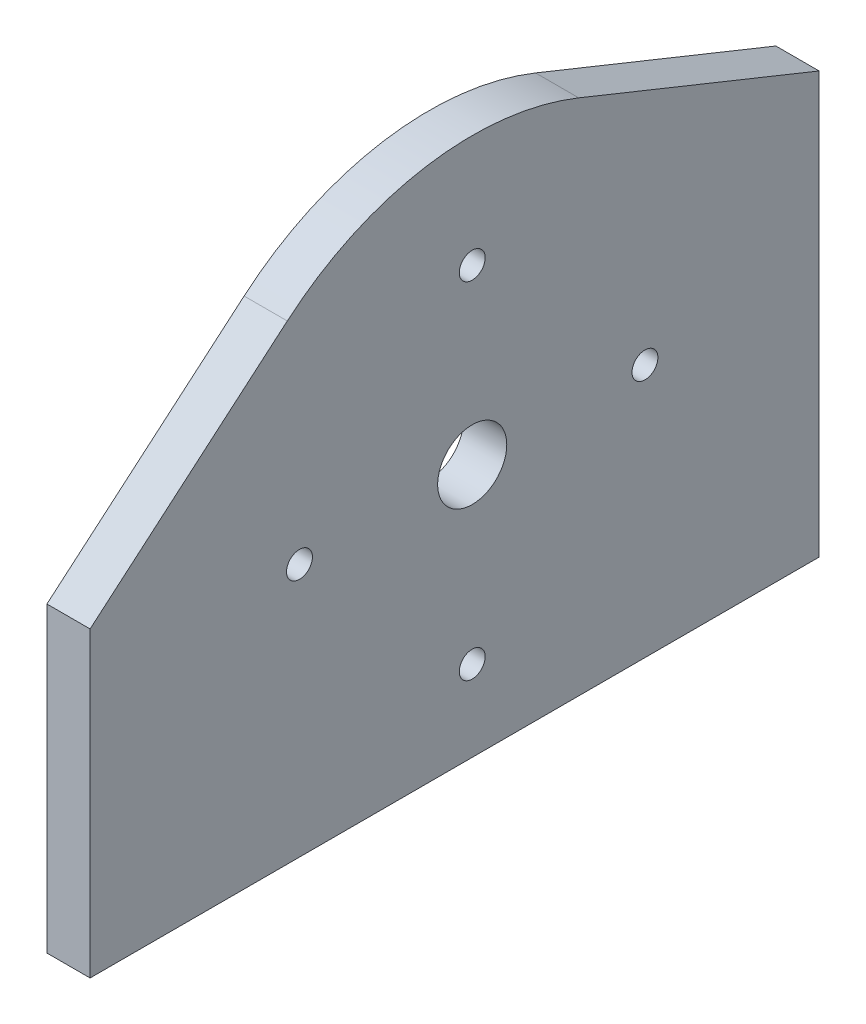
SolidWorks part; units mm, degrees
material "PMMA"
ref_plane "Piano frontale" through (0, 0, 0) normal (0, 0, 1) x (1, 0, 0)
ref_plane "Piano superiore" through (0, 0, 0) normal (0, 1, 0) x (1, 0, 0)
ref_plane "Piano destro" through (0, 0, 0) normal (1, 0, 0) x (0, 0, -1)
sketch "Model" plane through (0, 0, 0) normal (1, 0, 0) x (0, 0, -1)
  line L0 (67.9402, 99.4804) -> (217.5257, 99.4804)
  line L1 (217.5257, 99.4804) -> (217.5258, 94.516)
  line L2 (217.5258, 94.516) -> (67.9406, 94.5157)
  line L3 (67.9406, 94.5157) -> (67.9402, 99.4804)
  line L4 (75.701, 145.6492) -> (169.4508, 145.6492)
  line L5 (169.4508, 145.6492) -> (169.4508, 140.6845)
  line L6 (169.4508, 140.6845) -> (75.7013, 140.6845)
  line L7 (75.7013, 140.6845) -> (75.701, 145.6492)
  line L8 (277.8427, 54.3742) -> (278.3063, 54.3694)
  line L9 (278.3063, 54.3694) -> (7.5827, 54.3742)
  line L10 (-9.9912, 108.2246) -> (89.8382, 182.1486)
  line L11 (107.8333, 184.8972) -> (289.0756, 111.8678)
  line L12 (102.5827, 131.7594) -> (142.5827, 131.7594)
  line L13 (142.5827, 131.7594) -> (142.5827, 101.7594)
  line L14 (142.5827, 101.7594) -> (102.5827, 101.7594)
  line L15 (102.5827, 101.7594) -> (102.5827, 131.7594)
  spline S0 degree 3 poles (11.5524, 84.2317) (11.5524, 82.8135) (10.7957, 81.503) (9.5675, 80.7939) knots 0 0 0 0 1 1 1 1
  spline S1 degree 3 poles (9.5675, 80.7939) (8.3393, 80.0848) (6.8261, 80.0848) (5.5978, 80.7939) knots 0 0 0 0 1 1 1 1
  spline S2 degree 3 poles (5.5978, 80.7939) (4.3696, 81.503) (3.613, 82.8135) (3.613, 84.2317) knots 0 0 0 0 1 1 1 1
  spline S3 degree 3 poles (3.613, 84.2317) (3.613, 85.65) (4.3696, 86.9605) (5.5978, 87.6696) knots 0 0 0 0 1 1 1 1
  spline S4 degree 3 poles (5.5978, 87.6696) (6.8261, 88.3787) (8.3393, 88.3787) (9.5675, 87.6696) knots 0 0 0 0 1 1 1 1
  spline S5 degree 3 poles (9.5675, 87.6696) (10.7957, 86.9605) (11.5524, 85.65) (11.5524, 84.2317) knots 0 0 0 0 1 1 1 1
  spline S6 degree 3 poles (281.5524, 84.2317) (281.5524, 82.8135) (280.7957, 81.503) (279.5675, 80.7939) knots 0 0 0 0 1 1 1 1
  spline S7 degree 3 poles (279.5675, 80.7939) (278.3393, 80.0848) (276.826, 80.0848) (275.5978, 80.7939) knots 0 0 0 0 1 1 1 1
  spline S8 degree 3 poles (275.5978, 80.7939) (274.3696, 81.503) (273.613, 82.8135) (273.613, 84.2317) knots 0 0 0 0 1 1 1 1
  spline S9 degree 3 poles (273.613, 84.2317) (273.613, 85.65) (274.3696, 86.9605) (275.5978, 87.6696) knots 0 0 0 0 1 1 1 1
  spline S10 degree 3 poles (275.5978, 87.6696) (276.826, 88.3787) (278.3393, 88.3787) (279.5675, 87.6696) knots 0 0 0 0 1 1 1 1
  spline S11 degree 3 poles (279.5675, 87.6696) (280.7957, 86.9605) (281.5524, 85.65) (281.5524, 84.2317) knots 0 0 0 0 1 1 1 1
  spline S12 degree 3 poles (106.2634, 174.3826) (109.2777, 172.6422) (111.1346, 169.426) (111.1346, 165.9453) knots 0 0 0 0 1 1 1 1
  spline S13 degree 3 poles (111.1346, 165.9453) (111.1346, 162.4646) (109.2777, 159.2484) (106.2634, 157.508) knots 0 0 0 0 1 1 1 1
  spline S14 degree 3 poles (106.2634, 157.508) (103.249, 155.7677) (99.5352, 155.7677) (96.5208, 157.508) knots 0 0 0 0 1 1 1 1
  spline S15 degree 3 poles (96.5208, 157.508) (93.5065, 159.2484) (91.6496, 162.4646) (91.6496, 165.9453) knots 0 0 0 0 1 1 1 1
  spline S16 degree 3 poles (91.6496, 165.9453) (91.6496, 169.426) (93.5065, 172.6422) (96.5208, 174.3826) knots 0 0 0 0 1 1 1 1
  spline S17 degree 3 poles (96.5208, 174.3826) (99.5352, 176.1229) (103.249, 176.1229) (106.2634, 174.3826) knots 0 0 0 0 1 1 1 1
  spline S18 degree 3 poles (115.181, 160.1104) (115.7944, 159.7563) (116.1722, 159.1018) (116.1722, 158.3936) knots 0 0 0 0 1 1 1 1
  spline S19 degree 3 poles (116.1722, 158.3936) (116.1722, 157.6853) (115.7944, 157.0309) (115.181, 156.6768) knots 0 0 0 0 1 1 1 1
  spline S20 degree 3 poles (115.181, 156.6768) (114.5677, 156.3226) (113.812, 156.3226) (113.1986, 156.6768) knots 0 0 0 0 1 1 1 1
  spline S21 degree 3 poles (113.1986, 156.6768) (112.5852, 157.0309) (112.2074, 157.6853) (112.2074, 158.3936) knots 0 0 0 0 1 1 1 1
  spline S22 degree 3 poles (112.2074, 158.3936) (112.2074, 159.1018) (112.5852, 159.7563) (113.1986, 160.1104) knots 0 0 0 0 1 1 1 1
  spline S23 degree 3 poles (113.1986, 160.1104) (113.812, 160.4645) (114.5677, 160.4645) (115.181, 160.1104) knots 0 0 0 0 1 1 1 1
  spline S24 degree 3 poles (89.6889, 160.1104) (90.3022, 159.7563) (90.6801, 159.1018) (90.6801, 158.3936) knots 0 0 0 0 1 1 1 1
  spline S25 degree 3 poles (90.6801, 158.3936) (90.6801, 157.6853) (90.3022, 157.0309) (89.6889, 156.6768) knots 0 0 0 0 1 1 1 1
  spline S26 degree 3 poles (89.6889, 156.6768) (89.0755, 156.3226) (88.3198, 156.3226) (87.7065, 156.6768) knots 0 0 0 0 1 1 1 1
  spline S27 degree 3 poles (87.7065, 156.6768) (87.0931, 157.0309) (86.7153, 157.6853) (86.7153, 158.3936) knots 0 0 0 0 1 1 1 1
  spline S28 degree 3 poles (86.7153, 158.3936) (86.7153, 159.1018) (87.0931, 159.7563) (87.7065, 160.1104) knots 0 0 0 0 1 1 1 1
  spline S29 degree 3 poles (87.7065, 160.1104) (88.3198, 160.4645) (89.0755, 160.4645) (89.6889, 160.1104) knots 0 0 0 0 1 1 1 1
  spline S30 degree 3 poles (102.4349, 182.1873) (103.0483, 181.8331) (103.4262, 181.1787) (103.4262, 180.4704) knots 0 0 0 0 1 1 1 1
  spline S31 degree 3 poles (103.4262, 180.4704) (103.4262, 179.7622) (103.0483, 179.1077) (102.435, 178.7536) knots 0 0 0 0 1 1 1 1
  spline S32 degree 3 poles (102.435, 178.7536) (101.8216, 178.3995) (101.0659, 178.3995) (100.4525, 178.7536) knots 0 0 0 0 1 1 1 1
  spline S33 degree 3 poles (100.4525, 178.7536) (99.8392, 179.1077) (99.4613, 179.7622) (99.4613, 180.4704) knots 0 0 0 0 1 1 1 1
  spline S34 degree 3 poles (99.4613, 180.4704) (99.4613, 181.1787) (99.8392, 181.8331) (100.4525, 182.1873) knots 0 0 0 0 1 1 1 1
  spline S35 degree 3 poles (100.4525, 182.1873) (101.0659, 182.5414) (101.8216, 182.5414) (102.4349, 182.1873) knots 0 0 0 0 1 1 1 1
  spline S36 degree 3 poles (20.809, 96.941) (20.809, 97.6493) (21.1869, 98.3037) (21.8002, 98.6578) knots 0 0 0 0 1 1 1 1
  spline S37 degree 3 poles (21.8002, 98.6578) (22.4136, 99.012) (23.1693, 99.012) (23.7826, 98.6578) knots 0 0 0 0 1 1 1 1
  spline S38 degree 3 poles (23.7826, 98.6578) (24.396, 98.3037) (24.7739, 97.6493) (24.7739, 96.941) knots 0 0 0 0 1 1 1 1
  spline S39 degree 3 poles (24.7739, 96.941) (24.7739, 96.2328) (24.396, 95.5783) (23.7826, 95.2242) knots 0 0 0 0 1 1 1 1
  spline S40 degree 3 poles (23.7826, 95.2242) (23.1693, 94.8701) (22.4136, 94.8701) (21.8002, 95.2242) knots 0 0 0 0 1 1 1 1
  spline S41 degree 3 poles (21.8002, 95.2242) (21.1869, 95.5783) (20.809, 96.2328) (20.809, 96.941) knots 0 0 0 0 1 1 1 1
  spline S42 degree 3 poles (260.4931, 96.9408) (260.4931, 97.6491) (260.8709, 98.3035) (261.4843, 98.6577) knots 0 0 0 0 1 1 1 1
  spline S43 degree 3 poles (261.4843, 98.6577) (262.0976, 99.0118) (262.8533, 99.0118) (263.4667, 98.6577) knots 0 0 0 0 1 1 1 1
  spline S44 degree 3 poles (263.4667, 98.6577) (264.0801, 98.3035) (264.4579, 97.6491) (264.4579, 96.9408) knots 0 0 0 0 1 1 1 1
  spline S45 degree 3 poles (264.4579, 96.9408) (264.4579, 96.2326) (264.0801, 95.5781) (263.4667, 95.224) knots 0 0 0 0 1 1 1 1
  spline S46 degree 3 poles (263.4667, 95.224) (262.8533, 94.8699) (262.0976, 94.8699) (261.4843, 95.224) knots 0 0 0 0 1 1 1 1
  spline S47 degree 3 poles (261.4843, 95.224) (260.8709, 95.5781) (260.4931, 96.2326) (260.4931, 96.9408) knots 0 0 0 0 1 1 1 1
  spline S48 degree 3 poles (68.2691, 143.1669) (68.2691, 143.8751) (68.6469, 144.5296) (69.2603, 144.8837) knots 0 0 0 0 1 1 1 1
  spline S49 degree 3 poles (69.2603, 144.8837) (69.8737, 145.2378) (70.6294, 145.2378) (71.2427, 144.8837) knots 0 0 0 0 1 1 1 1
  spline S50 degree 3 poles (71.2427, 144.8837) (71.8561, 144.5296) (72.2339, 143.8751) (72.2339, 143.1669) knots 0 0 0 0 1 1 1 1
  spline S51 degree 3 poles (72.2339, 143.1669) (72.2339, 142.4586) (71.8561, 141.8042) (71.2427, 141.45) knots 0 0 0 0 1 1 1 1
  spline S52 degree 3 poles (71.2427, 141.45) (70.6294, 141.0959) (69.8737, 141.0959) (69.2603, 141.45) knots 0 0 0 0 1 1 1 1
  spline S53 degree 3 poles (69.2603, 141.45) (68.6469, 141.8042) (68.2691, 142.4586) (68.2691, 143.1669) knots 0 0 0 0 1 1 1 1
  spline S54 degree 3 poles (172.9986, 143.1669) (172.9986, 143.8751) (173.3764, 144.5296) (173.9898, 144.8837) knots 0 0 0 0 1 1 1 1
  spline S55 degree 3 poles (173.9898, 144.8837) (174.6032, 145.2378) (175.3589, 145.2378) (175.9722, 144.8837) knots 0 0 0 0 1 1 1 1
  spline S56 degree 3 poles (175.9722, 144.8837) (176.5856, 144.5296) (176.9634, 143.8751) (176.9634, 143.1669) knots 0 0 0 0 1 1 1 1
  spline S57 degree 3 poles (176.9634, 143.1669) (176.9634, 142.4586) (176.5856, 141.8042) (175.9722, 141.45) knots 0 0 0 0 1 1 1 1
  spline S58 degree 3 poles (175.9722, 141.45) (175.3589, 141.0959) (174.6032, 141.0959) (173.9898, 141.45) knots 0 0 0 0 1 1 1 1
  spline S59 degree 3 poles (173.9898, 141.45) (173.3764, 141.8042) (172.9986, 142.4586) (172.9986, 143.1669) knots 0 0 0 0 1 1 1 1
  spline S60 degree 3 poles (85.7246, 137.2262) (85.7246, 137.9345) (86.1025, 138.5889) (86.7159, 138.943) knots 0 0 0 0 1 1 1 1
  spline S61 degree 3 poles (86.7159, 138.943) (87.3292, 139.2972) (88.0849, 139.2972) (88.6983, 138.943) knots 0 0 0 0 1 1 1 1
  spline S62 degree 3 poles (88.6983, 138.943) (89.3116, 138.5889) (89.6895, 137.9345) (89.6895, 137.2262) knots 0 0 0 0 1 1 1 1
  spline S63 degree 3 poles (89.6895, 137.2262) (89.6895, 136.518) (89.3116, 135.8635) (88.6983, 135.5094) knots 0 0 0 0 1 1 1 1
  spline S64 degree 3 poles (88.6983, 135.5094) (88.0849, 135.1553) (87.3292, 135.1553) (86.7159, 135.5094) knots 0 0 0 0 1 1 1 1
  spline S65 degree 3 poles (86.7159, 135.5094) (86.1025, 135.8635) (85.7246, 136.518) (85.7246, 137.2262) knots 0 0 0 0 1 1 1 1
  spline S66 degree 3 poles (148.3215, 137.2262) (148.3215, 137.9345) (148.6994, 138.5889) (149.3127, 138.943) knots 0 0 0 0 1 1 1 1
  spline S67 degree 3 poles (149.3127, 138.943) (149.9261, 139.2972) (150.6818, 139.2972) (151.2952, 138.943) knots 0 0 0 0 1 1 1 1
  spline S68 degree 3 poles (151.2952, 138.943) (151.9085, 138.5889) (152.2864, 137.9345) (152.2864, 137.2262) knots 0 0 0 0 1 1 1 1
  spline S69 degree 3 poles (152.2864, 137.2262) (152.2864, 136.518) (151.9085, 135.8635) (151.2952, 135.5094) knots 0 0 0 0 1 1 1 1
  spline S70 degree 3 poles (151.2952, 135.5094) (150.6818, 135.1553) (149.9261, 135.1553) (149.3127, 135.5094) knots 0 0 0 0 1 1 1 1
  spline S71 degree 3 poles (149.3127, 135.5094) (148.6994, 135.8635) (148.3215, 136.518) (148.3215, 137.2262) knots 0 0 0 0 1 1 1 1
  spline S72 degree 3 poles (218.5454, 91.2336) (218.5454, 91.9418) (218.9232, 92.5963) (219.5366, 92.9504) knots 0 0 0 0 1 1 1 1
  spline S73 degree 3 poles (219.5366, 92.9504) (220.15, 93.3045) (220.9057, 93.3045) (221.519, 92.9504) knots 0 0 0 0 1 1 1 1
  spline S74 degree 3 poles (221.519, 92.9504) (222.1324, 92.5963) (222.5102, 91.9418) (222.5102, 91.2336) knots 0 0 0 0 1 1 1 1
  spline S75 degree 3 poles (222.5102, 91.2336) (222.5102, 90.5253) (222.1324, 89.8709) (221.519, 89.5168) knots 0 0 0 0 1 1 1 1
  spline S76 degree 3 poles (221.519, 89.5168) (220.9057, 89.1626) (220.15, 89.1626) (219.5366, 89.5168) knots 0 0 0 0 1 1 1 1
  spline S77 degree 3 poles (219.5366, 89.5168) (218.9232, 89.8709) (218.5454, 90.5253) (218.5454, 91.2336) knots 0 0 0 0 1 1 1 1
  spline S78 degree 3 poles (62.9042, 91.2341) (62.9042, 91.9423) (63.282, 92.5968) (63.8954, 92.9509) knots 0 0 0 0 1 1 1 1
  spline S79 degree 3 poles (63.8954, 92.9509) (64.5088, 93.305) (65.2645, 93.305) (65.8778, 92.9509) knots 0 0 0 0 1 1 1 1
  spline S80 degree 3 poles (65.8778, 92.9509) (66.4912, 92.5968) (66.869, 91.9423) (66.869, 91.2341) knots 0 0 0 0 1 1 1 1
  spline S81 degree 3 poles (66.869, 91.2341) (66.869, 90.5258) (66.4912, 89.8714) (65.8778, 89.5173) knots 0 0 0 0 1 1 1 1
  spline S82 degree 3 poles (65.8778, 89.5173) (65.2645, 89.1631) (64.5088, 89.1631) (63.8954, 89.5173) knots 0 0 0 0 1 1 1 1
  spline S83 degree 3 poles (63.8954, 89.5173) (63.282, 89.8714) (62.9042, 90.5258) (62.9042, 91.2341) knots 0 0 0 0 1 1 1 1
  spline S84 degree 3 poles (169.3736, 91.2336) (169.3736, 91.9418) (169.7514, 92.5963) (170.3648, 92.9504) knots 0 0 0 0 1 1 1 1
  spline S85 degree 3 poles (170.3648, 92.9504) (170.9781, 93.3045) (171.7338, 93.3045) (172.3472, 92.9504) knots 0 0 0 0 1 1 1 1
  spline S86 degree 3 poles (172.3472, 92.9504) (172.9605, 92.5963) (173.3384, 91.9418) (173.3384, 91.2336) knots 0 0 0 0 1 1 1 1
  spline S87 degree 3 poles (173.3384, 91.2336) (173.3384, 90.5253) (172.9605, 89.8709) (172.3472, 89.5168) knots 0 0 0 0 1 1 1 1
  spline S88 degree 3 poles (172.3472, 89.5168) (171.7338, 89.1626) (170.9781, 89.1626) (170.3648, 89.5168) knots 0 0 0 0 1 1 1 1
  spline S89 degree 3 poles (170.3648, 89.5168) (169.7514, 89.8709) (169.3736, 90.5253) (169.3736, 91.2336) knots 0 0 0 0 1 1 1 1
  spline S90 degree 3 poles (112.2515, 91.2336) (112.2515, 91.9418) (112.6293, 92.5963) (113.2427, 92.9504) knots 0 0 0 0 1 1 1 1
  spline S91 degree 3 poles (113.2427, 92.9504) (113.8561, 93.3045) (114.6118, 93.3045) (115.2251, 92.9504) knots 0 0 0 0 1 1 1 1
  spline S92 degree 3 poles (115.2251, 92.9504) (115.8385, 92.5963) (116.2163, 91.9418) (116.2163, 91.2336) knots 0 0 0 0 1 1 1 1
  spline S93 degree 3 poles (116.2163, 91.2336) (116.2163, 90.5253) (115.8385, 89.8709) (115.2251, 89.5168) knots 0 0 0 0 1 1 1 1
  spline S94 degree 3 poles (115.2251, 89.5168) (114.6118, 89.1626) (113.8561, 89.1626) (113.2427, 89.5168) knots 0 0 0 0 1 1 1 1
  spline S95 degree 3 poles (113.2427, 89.5168) (112.6293, 89.8709) (112.2515, 90.5253) (112.2515, 91.2336) knots 0 0 0 0 1 1 1 1
  spline S96 degree 3 poles (289.0756, 111.8678) (292.9178, 110.2369) (296.1347, 108.0507) (298.8362, 105.3491) knots 0 0 0 0 1 1 1 1
  spline S97 degree 3 poles (298.8362, 105.3491) (301.5378, 102.6475) (303.7241, 99.4306) (305.235, 95.8585) knots 0 0 0 0 1 1 1 1
  spline S98 degree 3 poles (305.235, 95.8585) (306.7459, 92.2864) (307.5813, 88.3591) (307.5813, 84.2367) knots 0 0 0 0 1 1 1 1
  spline S99 degree 3 poles (307.5813, 84.2367) (307.5813, 67.7468) (294.2137, 54.3791) (277.8427, 54.3742) knots 0 0 0 0 1 1 1 1
  spline S100 degree 3 poles (7.5827, 54.3742) (-8.766, 54.3791) (-22.1337, 67.7468) (-22.1337, 84.2367) knots 0 0 0 0 1 1 1 1
  spline S101 degree 3 poles (-22.1337, 84.2367) (-22.1337, 92.4816) (-18.7918, 99.946) (-13.3886, 105.3491) knots 0 0 0 0 1 1 1 1
  spline S102 degree 3 poles (-13.3886, 105.3491) (-12.0378, 106.6999) (-10.5582, 107.9219) (-9.9912, 108.2246) knots 0 0 0 0 1 1 1 1
  spline S103 degree 3 poles (89.8382, 182.1486) (90.5198, 182.6635) (91.6227, 183.3375) (92.7755, 183.8987) knots 0 0 0 0 1 1 1 1
  spline S104 degree 3 poles (92.7755, 183.8987) (93.9282, 184.4598) (95.1308, 184.9082) (96.3649, 185.2389) knots 0 0 0 0 1 1 1 1
  spline S105 degree 3 poles (96.3649, 185.2389) (97.5989, 185.5696) (98.8646, 185.7825) (100.1435, 185.8729) knots 0 0 0 0 1 1 1 1
  spline S106 degree 3 poles (100.1435, 185.8729) (101.4224, 185.9633) (102.7145, 185.9311) (104.0017, 185.7714) knots 0 0 0 0 1 1 1 1
  spline S107 degree 3 poles (104.0017, 185.7714) (105.2888, 185.6116) (106.5709, 185.3244) (107.8333, 184.8972) knots 0 0 0 0 1 1 1 1
sketch "Schizzo5" plane through (0, 0, 0) normal (1, 0, 0) x (0, 0, -1)
  line L0 (-95, 0) -> (201, 0) construction
  line L1 (0, 81) -> (0, 0) construction
  dimension "D1" = 95
  dimension "D2" = 201
  dimension "D3" = 81
sketch "Schizzo2" plane through (0, 0, 0) normal (1, 0, 0) x (0, 0, -1)
  line L0 (0, 101) -> (0, 61) construction
  line L1 (-20, 81) -> (20, 81) construction
  circle A0 centre (-95, 0) radius 4
  circle A1 centre (201, 0) radius 4
  circle A2 centre (0, 101) radius 1.5
  circle A3 centre (0, 61) radius 1.5
  circle A4 centre (20, 81) radius 1.5
  circle A5 centre (-20, 81) radius 1.5
  circle A6 centre (0, 81) radius 4
  point P9 (0, 81)
  point P12 (0, 81)
  dimension "D1" = 8
  dimension "D3" = 3
  dimension "D4" = 40
  dimension "D7" = 8
  dimension "D2" = 40
sketch "Schizzo3" plane through (0, 0, 0) normal (1, 0, 0) x (0, 0, -1)
  line L0 (40.1602, 51.6471) -> (40.1602, 100.3948)
  line L1 (213.3346, 30.6081) -> (12.3346, 111.6081) construction
  line L3 (-44.2392, 86.6471) -> (-21.4107, 106.1114)
  line L4 (40.1602, 100.3948) -> (12.3346, 111.6081)
  line L8 (-44.2392, 86.6471) -> (-44.2392, 51.6471)
  line L10 (-44.2392, 51.6471) -> (40.1602, 51.6471)
  arc A0 (12.3346, 111.6081) -> (-21.4107, 106.1114) centre (0, 81) ccw
  dimension "D3" = 30
  dimension "D14" = 30
  dimension "D15" = 35
extrude "Estrusione-Estrusione1" add sketch "Schizzo3" along normal blind 5
extrude "Taglio-Estrusione1" cut sketch "Schizzo2" along normal through all
equation "\"Thickness\"=5"
equation "\"D1@Estrusione-Estrusione1\"=\"Thickness\""
